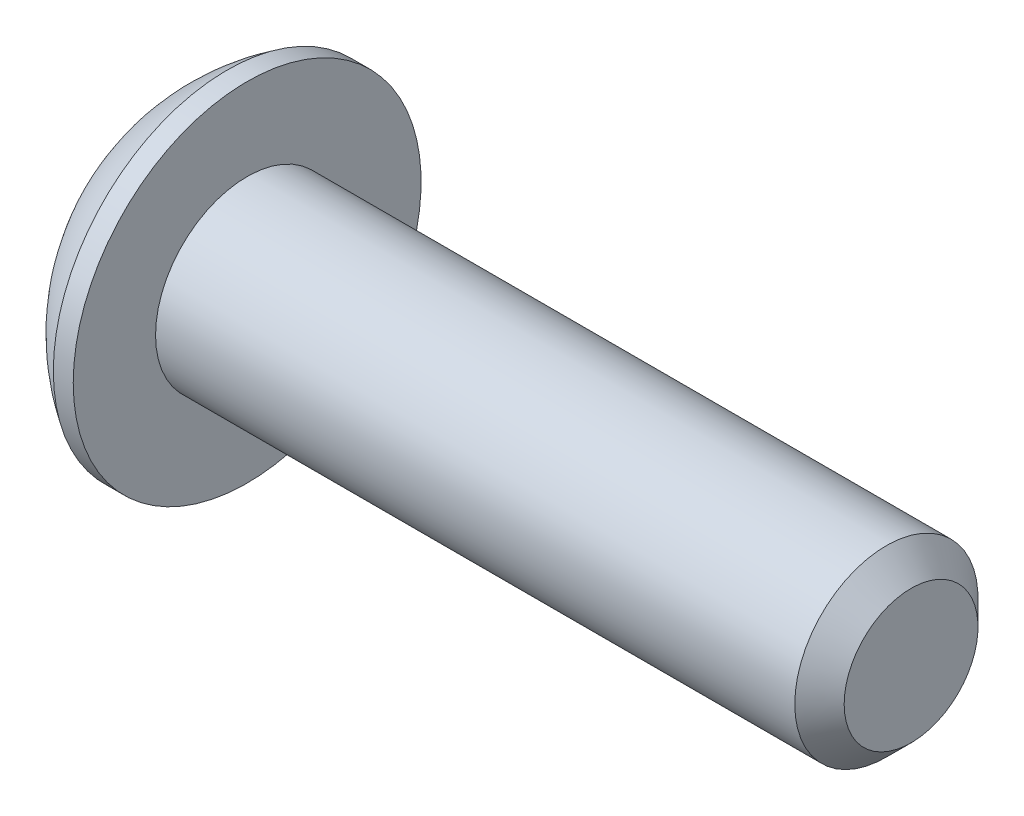
SolidWorks part; units mm, degrees
ref_plane "Plane1" through (0, 0, 0) normal (0, 0, 1) x (1, 0, 0)
ref_plane "Plane2" through (0, 0, 0) normal (0, 1, 0) x (1, 0, 0)
ref_plane "Plane3" through (0, 0, 0) normal (1, 0, 0) x (0, 0, -1)
sketch "BodySke" plane through (0, 0, 0) normal (0, 0, 1) x (1, 0, 0)
  line L0 (14.5542, 0) -> (14.5542, 1.2802)
  line L1 (14.0818, 1.7526) -> (1.8542, 1.7526)
  line L2 (1.8542, 1.7526) -> (1.8542, 3.3274)
  line L3 (1.8542, 3.3274) -> (1.4732, 3.3274)
  line L4 (0, 0) -> (101.6, 0) construction
  line L5 (1.8542, -3.3274) -> (1.4732, -3.3274) construction
  line L6 (55.6768, -1.7526) -> (1.8542, -1.7526) construction
  line L7 (14.5542, 0) -> (0, 0)
  line L8 (0, 1.6637) -> (0, -1.6637) construction
  line L9 (0, 0) -> (0, 1.6637)
  line L10 (14.5542, 1.2802) -> (14.0818, 1.7526)
  line L11 (14.5542, -1.2802) -> (14.0818, -1.7526) construction
  line L12 (2.6467, 9.525) -> (2.6467, -1.7526) construction
  line L13 (1.8542, 9.525) -> (1.8542, -1.7526) construction
  arc A1 (0, 1.6637) -> (1.4732, 3.3274) centre (3.5549, 0) cw
  dimension "D1" = 3.3274
  dimension "Diameter" = 3.5052
  dimension "Length" = 12.7
  dimension "Head_dia" = 6.6548
  dimension "Head_ht" = 1.8542
  dimension "Head_side_ht" = 0.381
  dimension "Minor_dia" = 2.5603
  dimension "Body_ch_ang" = 45
  dimension "Advance" = 0.7925
  dimension "Thread_nom" = 12.7
revolve "BaseBody" add sketch "BodySke" angle 360 about L4
cosmetic thread "ThreadCosmetic" [suppressed] parameters "Thread_length"=11.9075, "Thread_minor"=2.5603
sketch "Sketch2" plane through (0, 0, 0) normal (0, 0, 1) x (1, 0, 0)
  line L0 (0, 0.9906) -> (1.1176, 0.9906)
  line L1 (1.1176, 0.9906) -> (1.6895, 0)
  line L3 (1.6895, 0) -> (0, 0)
  line L4 (0, 0) -> (0, 0.9906)
  line L5 (0, -0.9906) -> (1.1176, -0.9906) construction
  line L6 (0, 0) -> (47.625, 0) construction
  dimension "D2" = 60
  dimension "PreBroach_depth" = 1.1176
  dimension "PreBroach_dia" = 1.9812
revolve "PreBroach" cut sketch "Sketch2" angle 360 about L6
sketch "Sketch3" plane through (0, 0, 0) normal (1, 0, 0) x (0, 0, -1)
  line L0 (-0.9906, -0.5719) -> (-0.9906, 0.5719)
  line L1 (-0.9906, 0.5719) -> (0, 1.1438)
  line L2 (0, 1.1438) -> (0.9906, 0.5719)
  line L3 (0.9906, 0.5719) -> (0.9906, -0.5719)
  line L4 (0.9906, -0.5719) -> (0, -1.1438)
  line L5 (0, -1.1438) -> (-0.9906, -0.5719)
  dimension "D1" = 0.9906
  dimension "D2" = 0.9906
  dimension "D3" = 1.9812
  dimension "Hex_size" = 1.9812
extrude "Hex" cut sketch "Sketch3" along normal blind 1.1176
sketch "Sketch4" plane through (0, 9.525, 0) normal (1, 0, 0) x (0, 0, -1)
  line L0 (0, -9.525) -> (1.2446, -9.525)
  line L1 (0, -9.525) -> (6.1484, -5.9752) construction
  line L2 (0, -9.525) -> (0.6223, -8.4471)
  line L3 (1.0085, -9.2654) -> (1.19, -9.1606)
  line L4 (0.7291, -8.7814) -> (0.9106, -8.6766)
  arc A0 (1.0085, -9.2654) -> (0.7291, -8.7814) centre (0, -9.525) ccw
  arc A1 (1.2446, -9.525) -> (1.19, -9.1606) centre (0, -9.525) ccw
  arc A2 (0.6223, -8.4471) -> (0.9106, -8.6766) centre (0, -9.525) cw
  dimension "D1" = 30
  dimension "Spline_n_dim" = 2.0828
  dimension "Spline_m_dim" = 2.4892
  dimension "D2" = 60
  dimension "D3" = 0.2794
  dimension "Spline_p_dim" = 0.5588
extrude "Spline" [suppressed] cut sketch "Sketch4" along normal blind 1.1176
pattern_circular "CirPattern1" [suppressed] count 6 every 60 about axis through (0, 0, 0) along (1, 0, 0)
sketch "ThdSchSke" plane through (0, 0, 0) normal (0, 0, 1) x (1, 0, 0)
  line L0 (2.6467, -1.2802) -> (2.3159, -1.7526)
  line L1 (2.6467, -1.2802) -> (2.9775, -1.7526)
  line L2 (2.9775, -1.7526) -> (2.9775, -2.1907)
  line L3 (-3.175, 0) -> (5.1513, 0) construction
  line L5 (2.9775, -2.1907) -> (2.3159, -2.1907)
  line L6 (2.3159, -2.1907) -> (2.3159, -1.7526)
  dimension "Thread_minor" = 2.5603
  dimension "Diameter" = 3.5052
  dimension "Start" = 2.6467
  dimension "SideAngle" = 55
  dimension "VeeAngle" = 70
  dimension "Overcut" = 4.3815
revolve "ThreadSchematic" [suppressed] cut sketch "ThdSchSke" angle 360 about L3
pattern_linear "ThdSchPat" [suppressed]
equation "\"D1@BodySke\" = \"Head_dia@BodySke\" * .5"
equation "\"Thread_minor@ThreadCosmetic\" = \"Minor_dia@BodySke\""
equation "\"D1@Sketch3\" = \"Hex_size@Sketch3\" / 2"
equation "\"D2@Sketch3\" = \"D1@Sketch3\""
equation "\"D3@Sketch3\" = \"Hex_size@Sketch3\""
equation "\"D3@Sketch4\" = \"Spline_p_dim@Sketch4\" / 2"
equation "\"D1@Sketch4\" = \"D2@Sketch4\" / 2"
equation "\"Thread_length@ThreadCosmetic\" = ((sgn( (\"Length@BodySke\" - \"Advance@BodySke\" ) - \"Thread_nom@BodySke\" )-1)*( (\"Length@BodySke\" - \"Advance@BodySke\" ) - \"Thread_nom@BodySke\" ))/-2+ \"Thread_nom@BodySke\""
equation "\"Thread_minor@ThdSchSke\" = \"Minor_dia@BodySke\""
equation "\"Diameter@ThdSchSke\" = \"Diameter@BodySke\""
equation "\"Overcut@ThdSchSke\" = \"Diameter@BodySke\" * 1.25"
equation "\"Start@ThdSchSke\" = \"Head_ht@BodySke\" + \"Length@BodySke\" - \"Thread_length@ThreadCosmetic\"  '---Non-countersunk---"
equation "\"Num_threads@ThdSchPat\" = int( \"Thread_length@ThreadCosmetic\" / \"Advance@BodySke\" + 0.999 )  + 1"
equation "\"Advance@ThdSchPat\" = \"Thread_length@ThreadCosmetic\" /  (\"Num_threads@ThdSchPat\" - 1) 'relax it"
equation "\"Num_threads@ThdSchPat\" = \"Num_threads@ThdSchPat\" - sgn( \"Num_threads@ThdSchPat\" - 1) '---chamfered tips only---"
